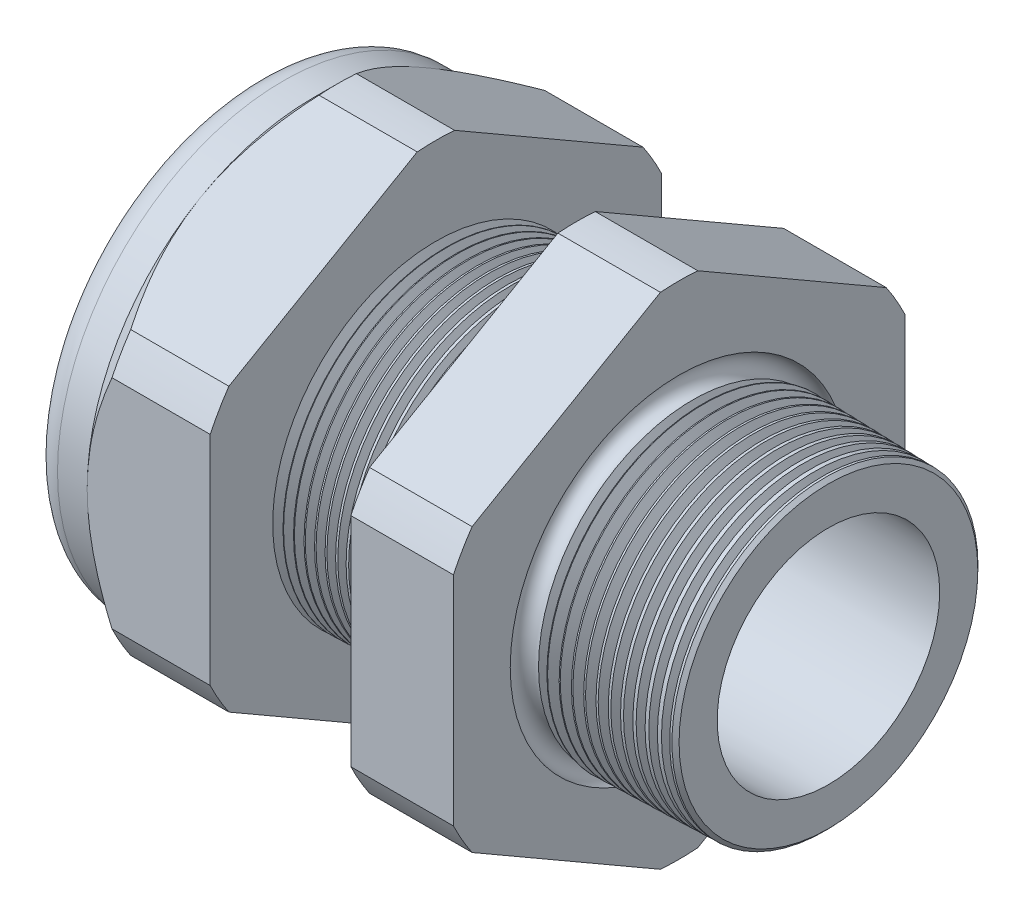
SolidWorks part; units mm, degrees
ref_plane "Front Plane" through (0, 0, 0) normal (0, 0, 1) x (1, 0, 0)
ref_plane "Top Plane" through (0, 0, 0) normal (0, 1, 0) x (1, 0, 0)
ref_plane "Right Plane" through (0, 0, 0) normal (1, 0, 0) x (0, 0, -1)
sketch "Sketch10" plane through (0, 0, 0) normal (0, 0, 1) x (1, 0, 0)
  line L0 (0, 0) -> (-115.3565, 0) construction
  line L1 (-38.862, 9.017) -> (-25.662, 9.017)
  line L2 (3.048, 8.1382) -> (3.048, 11.1862)
  line L3 (-7.874, 11.4722) -> (3.048, 11.1862)
  line L4 (-7.874, 33.02) -> (-7.874, 11.4722)
  line L5 (-7.874, 33.02) -> (-15.374, 33.02)
  line L6 (-15.374, 33.02) -> (-15.374, 11.6686)
  line L7 (-25.662, 11.938) -> (-15.374, 11.6686)
  line L8 (-25.662, 11.938) -> (-25.662, 33.02)
  line L9 (-25.662, 33.02) -> (-34.662, 33.02)
  line L10 (-34.662, 33.02) -> (-34.662, 16.51)
  line L11 (-34.662, 16.51) -> (-38.862, 16.51)
  line L12 (-38.862, 16.51) -> (-38.862, 9.017)
  line L13 (-25.662, 9.017) -> (3.048, 8.1382)
  dimension "D1" = 41.91
  dimension "D2" = 18.034
  dimension "D3" = 1.5
  dimension "D4" = 3.048
  dimension "A" = 23.876
  dimension "D6" = 33.02
  dimension "D8" = 66.04
  dimension "D9" = 4.2
  dimension "D10" = 9
  dimension "D11" = 7.5
  dimension "D" = 10.922
revolve "Revolve2" add sketch "Sketch10" angle 360 about L0
sketch "Sketch12" plane through (-34.662, 0, 0) normal (-1, 0, 0) x (0, 0, 1)
  line L1 (-1.3666, 18.2751) -> (-15.1434, 10.3211)
  line L2 (-16.51, 7.954) -> (-16.51, -7.954)
  line L3 (-15.1434, -10.3211) -> (-1.3666, -18.2751)
  line L4 (1.3666, -18.2751) -> (15.1434, -10.3211)
  line L5 (16.51, -7.954) -> (16.51, 7.954)
  line L6 (15.1434, 10.3211) -> (1.3666, 18.2751)
  circle A0 centre (0, 0) radius 16.51 construction
  arc A1 (1.3666, 18.2751) -> (-1.3666, 18.2751) centre (0, 0) ccw
  arc A2 (-15.1434, 10.3211) -> (-16.51, 7.954) centre (0, 0) ccw
  arc A3 (-16.51, -7.954) -> (-15.1434, -10.3211) centre (0, 0) ccw
  arc A4 (-1.3666, -18.2751) -> (1.3666, -18.2751) centre (0, 0) ccw
  arc A5 (15.1434, -10.3211) -> (16.51, -7.954) centre (0, 0) ccw
  arc A6 (16.51, 7.954) -> (15.1434, 10.3211) centre (0, 0) ccw
  dimension "D2" = 36.6522
  dimension "D1" = 33.02
extrude "Cut-Extrude2" cut sketch "Sketch12" against normal through all flip side to cut
fillet "Fillet4" radius 2.032 1 edges at (-38.862, 0, -16.51)
sketch "Sketch19" plane through (-34.662, 0, 0) normal (-1, 0, 0) x (0, 0, 1)
  line L0 (16.51, 0) -> (16.51, 7.954) construction
  circle A0 centre (0, 0) radius 16.51
extrude "Cut-Extrude3" cut sketch "Sketch19" against normal blind 3.998 draft 45 flip side to cut
chamfer "Chamfer1" distance 0.254 angle 45 1 edges at (3.048, 0, -11.1862)
sketch "Sketch21" plane through (-38.862, 0, 0) normal (-1, 0, 0) x (0, 0, 1)
  circle A0 centre (0, 0) radius 9.017
  circle A2 centre (0, 0) radius 9.017 construction
extrude "plug" add sketch "Sketch21" against normal blind 8.89 separate body
sketch "Sketch22" plane through (-38.862, 0, 0) normal (-1, 0, 0) x (0, 0, 1)
  circle A0 centre (0, 0) radius 8.763
  circle A1 centre (0, 0) radius 9.017 construction
  dimension "D1" = 0.254
extrude "Cut-Extrude4" cut sketch "Sketch22" against normal blind 0.508
sketch "Sketch27" plane through (-38.354, 0, 0) normal (-1, 0, 0) x (0, 0, 1)
  line L0 (-4.3624, 0) -> (4.3624, 0) construction
  circle A0 centre (-6.2128, 0) radius 2.54
  circle A1 centre (0, 0) radius 8.763 construction
  dimension "D1" = 0.0102
  dimension "holedia" = 5.08
extrude "plugholes" cut sketch "Sketch27" against normal through all
pattern_circular "CirPattern1" count 4 over 360 about axis through (0, 0, 0) along (1, 0, 0) of "plugholes"
sketch "Sketch28" [suppressed] plane through (-29.464, 0, 0) normal (-1, 0, 0) x (0, 0, 1)
  circle A0 centre (0, 0) radius 0.762
  dimension "midholedia" = 5.08
extrude "midhole" [suppressed] cut sketch "Sketch28" against normal through all
sketch "Sketch29" plane through (0, 0, 0) normal (0, 0, 1) x (1, 0, 0)
  line L0 (-25.662, 11.938) -> (-24.929, 11.9188)
  line L1 (-15.374, 11.6686) -> (-25.662, 11.938) construction
  line L2 (-24.929, 11.9188) -> (-25.3121, 11.2936)
  line L3 (-25.3121, 11.2936) -> (-25.662, 11.938)
  dimension "D1" = 60
  dimension "D2" = 60
  dimension "D3" = 0.635
revolve "Cut-Revolve1" cut sketch "Sketch29" angle 360 about axis through (0, 0, 0) along (-1, 0, 0)
pattern_linear "LPattern1" count 14 spacing 0.762 along (1, 0, 0) of "Cut-Revolve1"
sketch "Sketch30" plane through (0, 0, 0) normal (0, 0, 1) x (1, 0, 0)
  line L0 (-7.874, 11.4722) -> (-6.9944, 11.4492)
  line L1 (-7.874, 18.2751) -> (-7.874, 10.3211) construction
  line L2 (2.7941, 11.1929) -> (-7.874, 11.4722) construction
  line L3 (-6.9944, 11.4492) -> (-7.4542, 10.6989)
  line L4 (-7.4542, 10.6989) -> (-7.874, 11.4722)
  dimension "D1" = 60
  dimension "D2" = 60
  dimension "D3" = 0.762
revolve "Cut-Revolve2" cut sketch "Sketch30" angle 360 about axis through (0, 0, 0) along (-1, 0, 0)
pattern_linear "LPattern2" count 12 spacing 0.889 along (1, 0, 0) of "Cut-Revolve2"
sketch "Sketch31" [suppressed] plane through (-38.354, 0, 0) normal (-1, 0, 0) x (0, 0, 1)
  line L0 (-1.905, 1.905) -> (1.905, 1.905)
  line L1 (-1.905, -1.905) -> (1.905, -1.905)
  circle A0 centre (0, 0) radius 1.905 construction
  arc A1 (-1.905, 1.905) -> (-1.905, -1.905) centre (-1.905, 0) ccw
  arc A2 (1.905, 1.905) -> (1.905, -1.905) centre (1.905, 0) cw
extrude "Cut-Extrude5" [suppressed] cut sketch "Sketch31" against normal through all
sketch "Sketch32" plane through (0, 0, 0) normal (0, 0, 1) x (1, 0, 0)
  line L0 (-7.874, 18.2751) -> (-7.874, 10.3211) construction
  circle A0 centre (-7.747, 11.4722) radius 0.889
  dimension "D2" = 1.778
  dimension "D1" = 0.127
revolve "Cut-Revolve3" cut sketch "Sketch32" angle 360 about axis through (0, 0, 0) along (-1, 0, 0)
